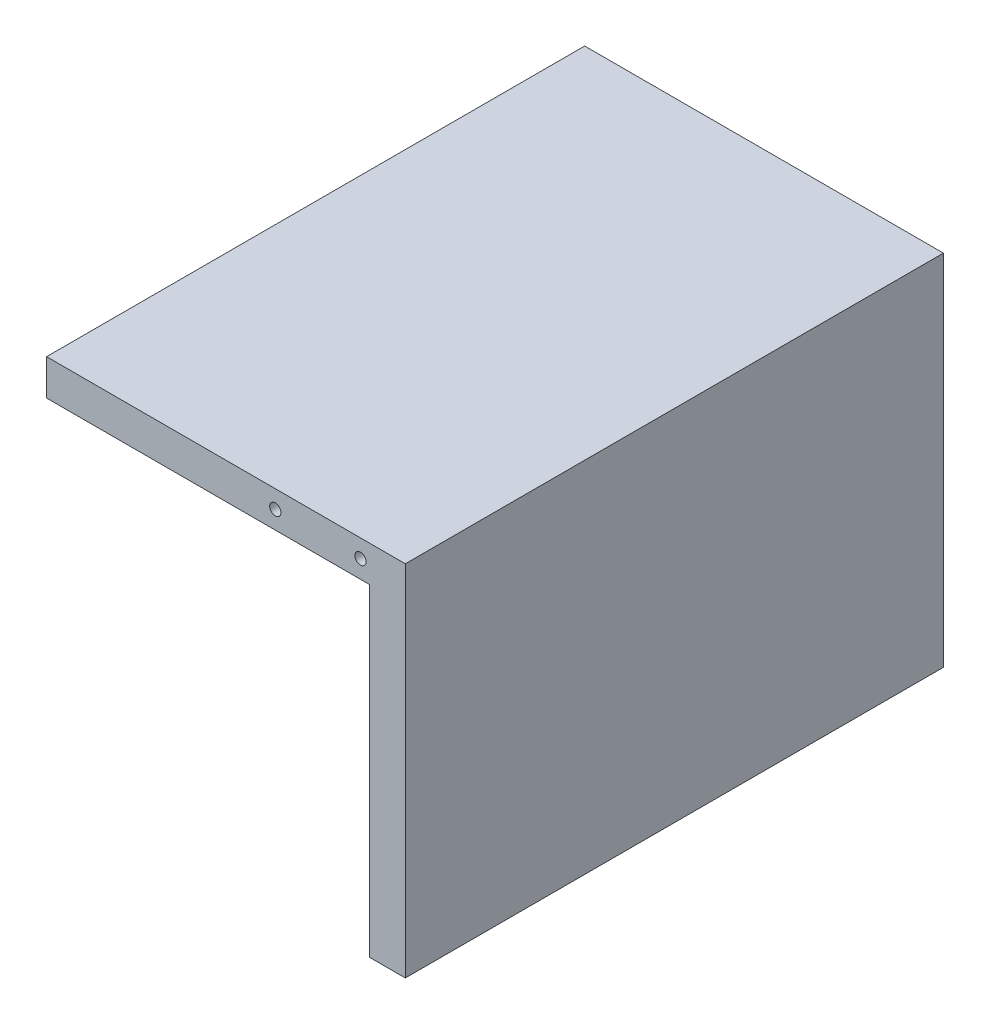
SolidWorks part; units mm, degrees
material "Lega 1060"
ref_plane "Piano frontale" through (0, 0, 0) normal (0, 0, 1) x (1, 0, 0)
ref_plane "Piano superiore" through (0, 0, 0) normal (0, 1, 0) x (1, 0, 0)
ref_plane "Piano destro" through (0, 0, 0) normal (1, 0, 0) x (0, 0, -1)
sketch "Schizzo1" plane through (0, 0, 0) normal (0, 0, 1) x (1, 0, 0)
  line L0 (0, 0) -> (-80, 0)
  line L1 (-80, 0) -> (-80, -8)
  line L2 (-80, -8) -> (-8, -8)
  line L3 (-8, -8) -> (-8, -80)
  line L4 (-8, -80) -> (0, -80)
  line L5 (0, -80) -> (0, 0)
  dimension "D1" = 80
  dimension "D2" = 80
  dimension "D3" = 8
  dimension "D4" = 8
extrude "Estrusione-Estrusione1" add sketch "Schizzo1" along normal blind 120
sketch "Schizzo15" plane through (0, 0, 120) normal (0, 0, 1) x (1, 0, 0)
  line L0 (-80, -4) -> (0, -4) construction
  line L1 (-80, 0) -> (-80, -8) construction
  line L2 (0, -80) -> (0, 0) construction
  point P6 (-10, -4)
  point P7 (-29, -4)
  dimension "D1" = 10
  dimension "D2" = 19
hole_wizard "Foro filettato M3-1" positions "Schizzo17" profile "Schizzo16" tap size "M3" standard "ISO"
sketch "Schizzo17" plane through (0, 0, 120) normal (0, 0, 1) x (1, 0, 0)
  point P0 (-10, -4)
  point P3 (-29, -4)
sketch "Schizzo16" plane through (-10, -4, 120) normal (1, 0, 0) x (0, -1, 0)
  line L0 (0, 0) -> (0, 10.7511)
  line L1 (0, 10.7511) -> (1.25, 10)
  line L2 (1.25, 10) -> (1.25, 0)
  line L5 (1.25, 0) -> (0, 0)
  line L10 (0, 10.7511) -> (-1.25, 10) construction
  line L11 (0, -6.35) -> (0, 107.95) construction
  dimension "Tap Drill Dia." = 2.5
  dimension "Tap Drill Depth" = 10
  dimension "Drill Angle" = 118
cosmetic thread "Filettatura del foro1" parameters "D1"=8, "D2"=3
cosmetic thread "Filettatura del foro2" parameters "D1"=8, "D2"=3
sketch "Sketch1" plane through (0, 0, 0) normal (1, 0, 0) x (0, 0, -1)
  line L0 (0, -80) -> (0, 0) construction
  point P0 (0, -8)
  dimension "D1" = 8
